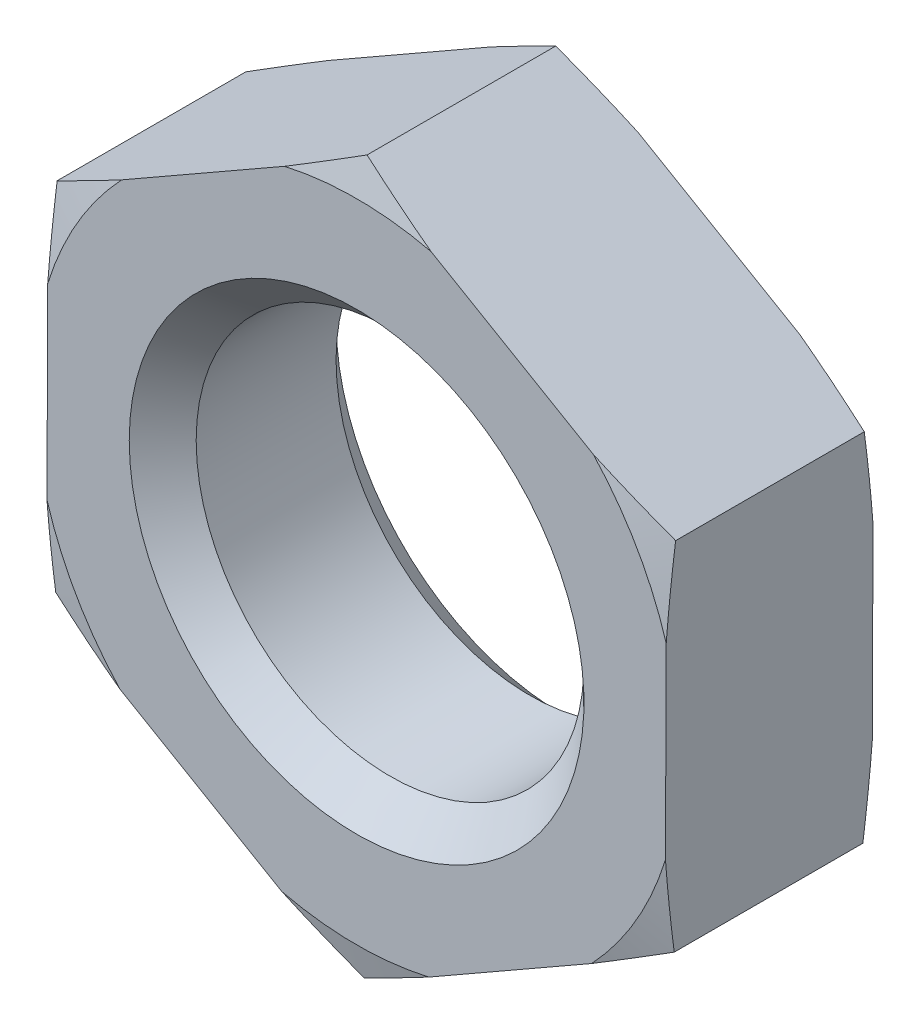
SolidWorks part; units mm, degrees
extrude "基体-拉伸" add sketch "草图1" along normal blind 3.2
sketch "草图1" plane through (0, 0, 0) normal (0, 0, 1) x (1, 0, 0)
  line L0 (-26.8088, 0) -> (37.1748, 0) construction
  line L1 (0, 25.0215) -> (0, -25.0215) construction
  line L3 (0.0217, 5.525) -> (-4.7739, 2.7813)
  line L4 (-4.7739, 2.7813) -> (-4.7956, -2.7437)
  line L5 (-4.7956, -2.7437) -> (-0.0217, -5.525)
  line L6 (-0.0217, -5.525) -> (4.7739, -2.7813)
  line L7 (4.7739, -2.7813) -> (4.7956, 2.7437)
  line L8 (4.7956, 2.7437) -> (0.0217, 5.525)
  circle A0 centre (0, 0) radius 4.7848 construction
  circle A1 centre (0, 0) radius 3
  dimension "D" = 6
  dimension "e" = 11.05
cosmetic thread "装饰螺纹线1"
chamfer "倒角1" distance 0.5179 angle 45 2 edges at (3, 0, 0) (3, 0, 3.2)
material "04级"
ref_plane "基准面1" through (0, 0, 0) normal (0, 0, 1) x (1, 0, 0)
ref_plane "基准面2" through (0, 0, 0) normal (0, 1, 0) x (1, 0, 0)
ref_plane "基准面3" through (0, 0, 0) normal (1, 0, 0) x (0, 0, -1)
sketch "尺寸草图" plane through (0, 0, 0) normal (0, 0, 1) x (1, 0, 0)
  line L0 (0, 0) -> (24.1005, 0)
  line L1 (0, 0) -> (6.75, 0)
  line L2 (46.8781, 0) -> (55.7781, 0)
  line L3 (-5.7143, 0) -> (0, 0)
  point P3 (6, 0)
  point P4 (2.5, 0)
  point P5 (11.05, 0)
  point P6 (3.2, 0)
  point P7 (7.3, 0)
  point P8 (10, 0)
  dimension "D" = 6
  dimension "e" = 11.05
  dimension "P" = 2.5
  dimension "m" = 3.2
  dimension "mw" = 7.3
  dimension "s" = 10
  dimension "da" = 6.75
  dimension "dw" = 8.9
  dimension "D1" = 5.7143
sketch "草图2" plane through (0, 0, 0) normal (0, 0, -1) x (-1, 0, 0)
  circle A0 centre (0, 0) radius 5
  circle A1 centre (0, 0) radius 3 construction
  dimension "s" = 10
extrude "切除-拉伸1" cut sketch "草图2" against normal through all draft 75 flip side to cut
sketch "草图3" plane through (0, 0, 3.2) normal (0, 0, 1) x (1, 0, 0)
  circle A0 centre (0, 0) radius 5
  dimension "D1" = 10
extrude "切除-拉伸2" cut sketch "草图3" against normal through all draft 75 flip side to cut
equation "\"e@草图1\" = \"e@尺寸草图\""
equation "\"D1@尺寸草图\" = \"D@尺寸草图\" / 1.05"
equation "\"D@草图1\" = \"D@尺寸草图\""
equation "\"m@基体-拉伸\" = \"m@尺寸草图\""
equation "\"D1@草图3\" = \"s@尺寸草图\""
equation "\"s@草图2\" = \"s@尺寸草图\""
equation "\"D2@装饰螺纹线1\" = 1.05 * \"D1@尺寸草图\""
equation "\"D1@倒角1\" =  ( \"da@尺寸草图\" - \"D1@尺寸草图\" )  / 2"
